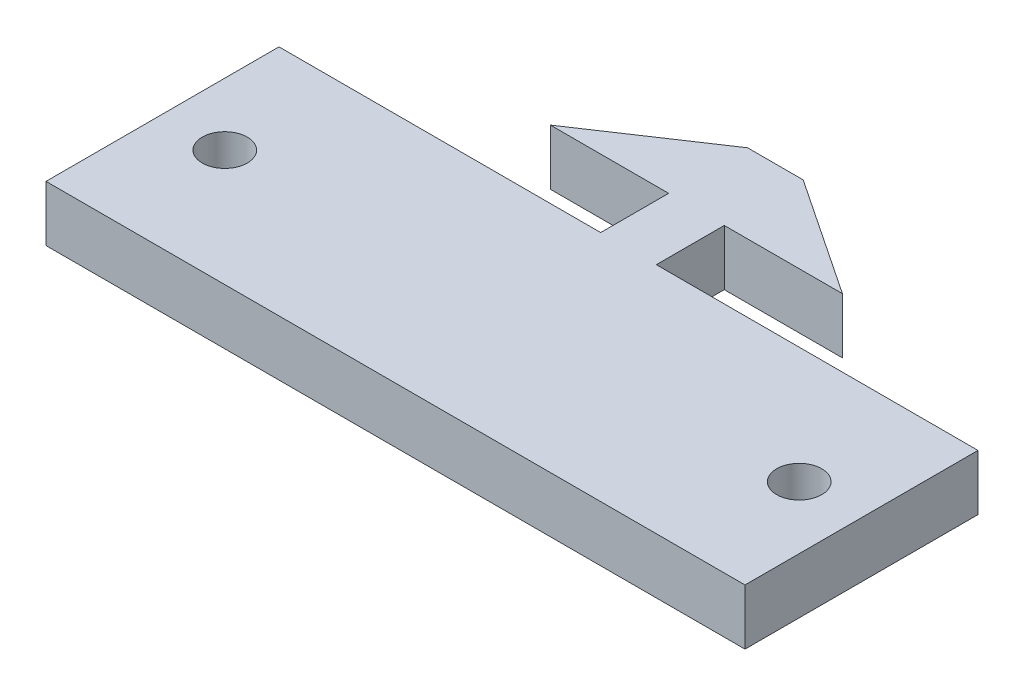
SolidWorks part; units mm, degrees
ref_plane "Front" through (0, 0, 0) normal (0, 0, 1) x (1, 0, 0)
ref_plane "Top" through (0, 0, 0) normal (0, 1, 0) x (1, 0, 0)
ref_plane "Right" through (0, 0, 0) normal (1, 0, 0) x (0, 0, -1)
sketch "Sketch1" plane through (0, 0, 0) normal (0, 1, 0) x (1, 0, 0)
  line L0 (-1.7907, 2.1875) -> (-9.398, 2.1875)
  line L2 (-1.7907, -2.1875) -> (-1.7907, 2.1875)
  line L4 (1.7907, -2.1875) -> (1.7907, 2.1875)
  line L7 (-9.398, 2.1875) -> (-1.7907, 7.2675)
  line L8 (-1.7907, 7.2675) -> (1.7907, 7.2675)
  line L9 (1.7907, 7.2675) -> (9.398, 2.1875)
  line L10 (9.398, 2.1875) -> (1.7907, 2.1875)
  line L11 (1.7907, -2.1875) -> (22.5, -2.1875)
  line L12 (-1.7907, -2.1875) -> (-22.5, -2.1875)
  line L13 (-22.5, -2.1875) -> (-22.5, -17.1875)
  line L14 (-22.5, -17.1875) -> (22.5, -17.1875)
  line L15 (22.5, -17.1875) -> (22.5, -2.1875)
  line L16 (22.5, -2.1875) -> (1.7907, -2.1875)
  point P0 (0, 0)
  point P17 (0, 7.2675)
  point P19 (0, -17.1875)
  point P24 (1.7907, 0)
  dimension "D1" = 18.796
  dimension "D2" = 3.5814
  dimension "D3" = 45
  dimension "D4" = 15
  dimension "D5" = 5.08
  dimension "D7" = 4.375
extrude "Boss-Extrude1" add sketch "Sketch1" along normal blind 3.5814 contours L14 L15 L11 L4 L10 L9 L8 L7 L0 L2 L12 L13
sketch "Sketch2" plane through (0, 3.5814, 0) normal (0, 1, 0) x (1, 0, 0)
  line L0 (0, 0) -> (0, -15.3387) construction
  line L2 (-22.5, -2.1875) -> (-22.5, -17.1875) construction
  circle A0 centre (-18.49, -9.6875) radius 1.45
  circle A1 centre (18.49, -9.6875) radius 1.45
  point P11 (-22.5, -9.6875)
  dimension "D1" = 2.9
  dimension "D2" = 18.49
extrude "Cut-Extrude1" cut sketch "Sketch2" against normal through all
